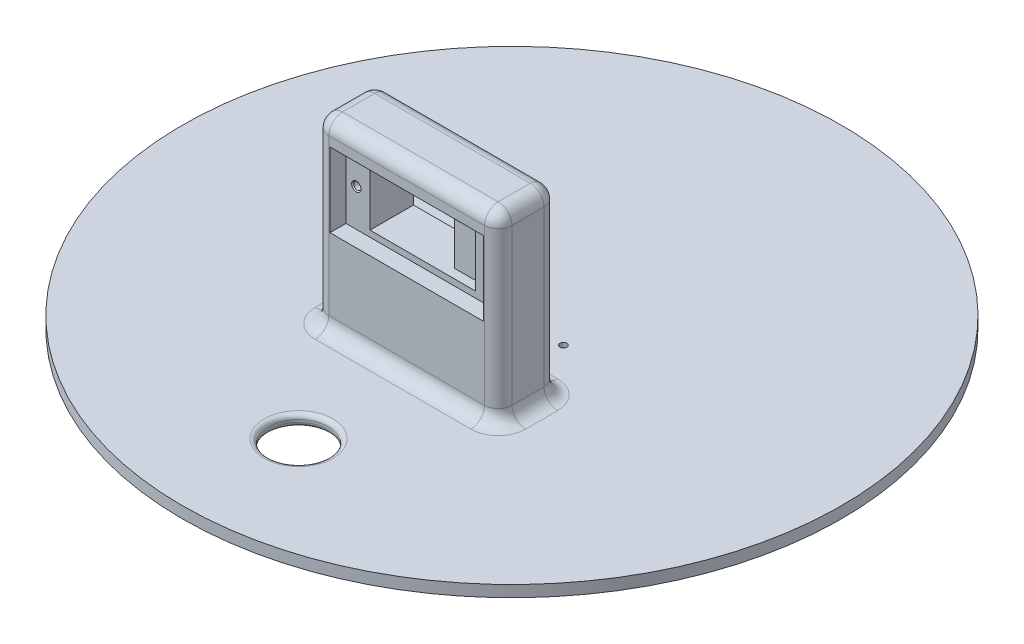
SolidWorks part; units mm, degrees
ref_plane "Front Plane" through (0, 0, 0) normal (0, 0, 1) x (1, 0, 0)
ref_plane "Top Plane" through (0, 0, 0) normal (0, 1, 0) x (1, 0, 0)
ref_plane "Right Plane" through (0, 0, 0) normal (1, 0, 0) x (0, 0, -1)
sketch "Sketch1" plane through (0, 0, 0) normal (0, 1, 0) x (1, 0, 0)
  circle A0 centre (0, 0) radius 72
  dimension "D1" = 144
extrude "Boss-Extrude1" add sketch "Sketch1" along normal blind 2.5
sketch "Sketch2" plane through (0, 0, 0) normal (0, -1, 0) x (-1, 0, 0)
  circle A0 centre (-11.25, 0) radius 0.75
  circle A1 centre (11.25, 0) radius 0.75
  dimension "D3" = 1.5
  dimension "D4" = 1.5
  dimension "D1" = 11.25
  dimension "D2" = 11.25
extrude "Cut-Extrude1" cut sketch "Sketch2" against normal blind 2.5
sketch "Sketch5" plane through (0, 2.5, 0) normal (0, 1, 0) x (1, 0, 0)
  line L0 (0, -1000) -> (0, 49000) construction
  line L1 (-1000, 0) -> (49000, 0) construction
  line L3 (-20, -5) -> (20, -5)
  line L4 (-20, -5) -> (-20, -23)
  line L5 (-20, -23) -> (20, -23)
  line L6 (20, -5) -> (20, -23)
  dimension "20" = 20
  dimension "D2" = 40
  dimension "D3" = 18
  dimension "D4" = 5
extrude "Boss-Extrude3" add sketch "Sketch5" along normal blind 40
sketch "Sketch6" plane through (0, 0, 23) normal (0, 0, 1) x (1, 0, 0)
  line L0 (-20, 42.5) -> (-20, 2.5) construction
  line L1 (-16.75, 37.4997) -> (16.75, 37.4997)
  line L2 (-16.75, 37.4997) -> (-16.75, 21.2796)
  line L3 (-16.75, 21.2796) -> (16.75, 21.2796)
  line L4 (16.75, 37.4997) -> (16.75, 21.2796)
  dimension "D1" = 33.5
  dimension "D2" = 3.25
extrude "Cut-Extrude2" cut sketch "Sketch6" against normal blind 3.5
sketch "Sketch7" plane through (0, 0, 19.5) normal (0, 0, 1) x (1, 0, 0)
  line L0 (16.75, 37.4997) -> (-16.75, 37.4997) construction
  line L1 (-11.5, 37.4997) -> (11.5, 37.4997)
  line L2 (-11.5, 37.4997) -> (-11.5, 21.2796)
  line L3 (-11.5, 21.2796) -> (11.5, 21.2796)
  line L4 (11.5, 37.4997) -> (11.5, 21.2796)
  line L5 (-16.75, 21.2796) -> (16.75, 21.2796) construction
  line L6 (-16.75, 37.4997) -> (-16.75, 21.2796) construction
  line L7 (16.75, 21.2796) -> (16.75, 37.4997) construction
  dimension "D1" = 5.25
  dimension "D2" = 5.25
extrude "Cut-Extrude3" cut sketch "Sketch7" against normal blind 2
sketch "Sketch8" plane through (0, 0, 17.5) normal (0, 0, 1) x (1, 0, 0)
  line L0 (-11.5, 21.2796) -> (11.5, 21.2796) construction
  line L1 (-11.5, 37.4997) -> (5, 37.4997)
  line L2 (-11.5, 37.4997) -> (-11.5, 21.2796)
  line L3 (-11.5, 21.2796) -> (5, 21.2796)
  line L4 (5, 37.4997) -> (5, 21.2796)
  dimension "D1" = 16.5
extrude "Cut-Extrude4" cut sketch "Sketch8" against normal blind 7
sketch "Sketch9" plane through (20, 0, 0) normal (1, 0, 0) x (0, 0, -1)
  line L0 (-23, 2.5) -> (-5, 2.5) construction
  line L1 (-5, 42.5) -> (-10, 42.5)
  line L2 (-5, 42.5) -> (-5, 2.5)
  line L3 (-5, 2.5) -> (-10, 2.5)
  line L4 (-10, 42.5) -> (-10, 2.5)
  dimension "D1" = 5
extrude "Cut-Extrude5" cut sketch "Sketch9" against normal through all
sketch "Sketch10" plane through (0, 0, 10.5) normal (0, 0, 1) x (1, 0, 0)
  line L1 (-11.5, 37.4997) -> (5, 37.4997)
  line L2 (-11.5, 37.4997) -> (-11.5, 21.2796)
  line L3 (-11.5, 21.2796) -> (5, 21.2796)
  line L4 (5, 37.4997) -> (5, 21.2796)
extrude "Cut-Extrude6" cut sketch "Sketch10" against normal through all
sketch "Sketch13" plane through (0, 0, 19.5) normal (0, 0, 1) x (1, 0, 0)
  line L0 (16.75, 21.2796) -> (16.75, 37.4997) construction
  line L1 (-16.75, 37.4997) -> (16.75, 37.4997)
  line L2 (-16.75, 37.4997) -> (-16.75, 36.1397)
  line L3 (-16.75, 36.1397) -> (16.75, 36.1397)
  line L4 (16.75, 37.4997) -> (16.75, 36.1397)
  line L6 (-16.75, 21.2796) -> (16.75, 21.2796)
  line L7 (-16.75, 21.2796) -> (-16.75, 22.6396)
  line L8 (-16.75, 22.6396) -> (16.75, 22.6396)
  line L9 (16.75, 21.2796) -> (16.75, 22.6396)
  dimension "D1" = 1.36
  dimension "D2" = 1.36
extrude "Boss-Extrude4" add sketch "Sketch13" against normal blind 9.5
hole_wizard "M2x0.4 Tapped Hole1" positions "Sketch14" profile "Sketch15" tap size "M2x0.4" standard "ANSI Metric"
sketch "Sketch14" plane through (0, 0, 19.5) normal (0, 0, 1) x (1, 0, 0)
  line L2 (-11.5, 36.1397) -> (11.5, 36.1397) construction
  line L3 (16.75, 21.2796) -> (16.75, 37.4997) construction
  line L4 (-16.75, 37.4997) -> (-16.75, 21.2796) construction
  point P0 (14.5, 29.3897)
  point P2 (-14.5, 29.3897)
  dimension "D1" = 6.75
  dimension "D2" = 6.75
  dimension "D3" = 2.25
  dimension "D4" = 2.25
sketch "Sketch15" plane through (14.5, 29.3897, 19.5) normal (1, 0, 0) x (0, -1, 0)
  line L0 (0, 0) -> (0, 6.4807)
  line L1 (0, 6.4807) -> (0.8, 6)
  line L2 (0.8, 6) -> (0.8, 0.225)
  line L3 (0.8, 0.225) -> (1.025, 0)
  line L5 (1.025, 0) -> (0, 0)
  line L6 (-0.8, 0.225) -> (-1.025, 0) construction
  line L10 (0, 6.4807) -> (-0.8, 6) construction
  line L11 (0, -6.35) -> (0, 107.95) construction
  dimension "Tap Drill Dia." = 1.6
  dimension "Tap Drill Depth" = 6
  dimension "Near C'Sink Dia." = 2.05
  dimension "Near C'Sink Angle" = 90
  dimension "Drill Angle" = 118
cosmetic thread "Hole Thread1" parameters "D1"=4, "D2"=2
cosmetic thread "Hole Thread2" parameters "D1"=4, "D2"=2
fillet "Fillet1" radius 3 4 edges at (20, 22.5, 23) (-20, 22.5, 23) (-20, 22.5, 10) (20, 22.5, 10)
fillet "Fillet2" radius 3 8 edges at (-19.1213, 2.5, 10.8787) (-20, 2.5, 16.5) (-19.1213, 2.5, 22.1213) (0, 2.5, 23) (19.1213, 2.5, 22.1213) (20, 2.5, 16.5) (19.1213, 2.5, 10.8787) (0, 2.5, 10)
fillet "Fillet3" radius 3 8 edges at (-19.1213, 42.5, 22.1213) (-20, 42.5, 16.5) (-19.1213, 42.5, 10.8787) (0, 42.5, 10) (19.1213, 42.5, 10.8787) (20, 42.5, 16.5) (19.1213, 42.5, 22.1213) (0, 42.5, 23)
sketch "Sketch16" plane through (0, 2.5, 0) normal (0, 1, 0) x (1, 0, 0)
  circle A0 centre (0, -46.6144) radius 6.5
  dimension "D1" = 13
extrude "Cut-Extrude7" cut sketch "Sketch16" against normal through all
fillet "Fillet4" radius 1 2 edges at (0, 0, 53.1144) (0, 2.5, 53.1144)
sketch "Sketch17" plane through (0, 2.5, 0) normal (0, 1, 0) x (1, 0, 0)
  circle A0 centre (4.75, 0) radius 0.75
  circle A1 centre (-4.75, 0) radius 0.75
  dimension "D1" = 1.5
  dimension "D2" = 1.5
  dimension "D3" = 4.75
  dimension "D4" = 4.75
extrude "Cut-Extrude8" cut sketch "Sketch17" against normal through all
